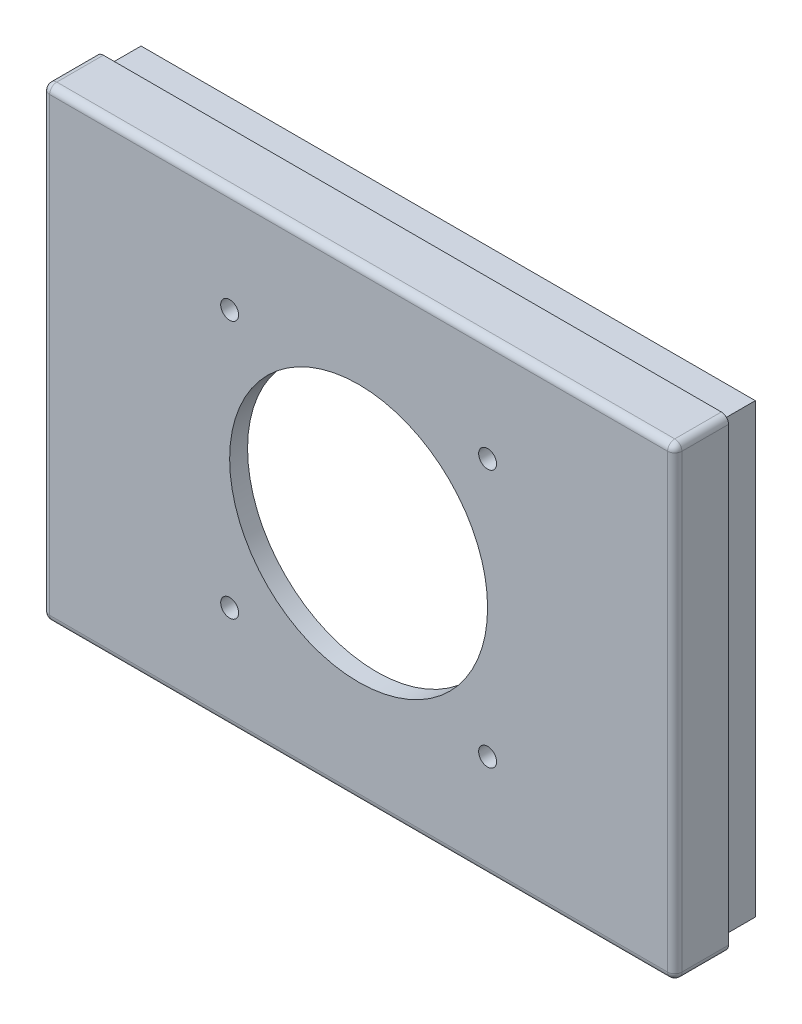
SolidWorks part; units mm, degrees
ref_plane "Front Plane" through (0, 0, 0) normal (0, 0, 1) x (1, 0, 0)
ref_plane "Top Plane" through (0, 0, 0) normal (0, 1, 0) x (1, 0, 0)
ref_plane "Right Plane" through (0, 0, 0) normal (1, 0, 0) x (0, 0, -1)
sketch "Sketch4" plane through (0, 0, 10) normal (0, 0, 1) x (1, 0, 0)
  line L1 (-25, 104.883) -> (151.492, 104.883)
  line L2 (-25, 104.883) -> (-25, -25)
  line L3 (-25, -25) -> (151.492, -25)
  line L4 (151.492, 104.883) -> (151.492, -25)
extrude "Boss-Extrude1" add sketch "Sketch4" along normal blind 25
sketch "Sketch5" plane through (0, 0, 10) normal (0, 0, -1) x (-1, 0, 0)
  line L0 (-146.492, 99.883) -> (-146.492, -20)
  line L1 (-151.492, 104.883) -> (25, 104.883)
  line L2 (-151.492, 104.883) -> (-151.492, -25)
  line L3 (-151.492, -25) -> (25, -25)
  line L4 (25, 104.883) -> (25, -25)
  line L5 (-146.492, -20) -> (20, -20)
  line L6 (20, 99.883) -> (20, -20)
  line L7 (-146.492, 99.883) -> (20, 99.883)
  dimension "D1" = 5
extrude "Cut-Extrude1" cut sketch "Sketch5" against normal blind 20 flip side to cut
sketch "Sketch7" plane through (0, 0, 10) normal (0, 0, -1) x (-1, 0, 0)
  line L0 (25, -25) -> (-151.492, -25) construction
  line L1 (-151.492, 104.883) -> (25, 104.883)
  line L2 (-151.492, 104.883) -> (-151.492, -25)
  line L3 (-151.492, -25) -> (25, -25)
  line L4 (25, 104.883) -> (25, -25)
  line L5 (-148.972, 102.363) -> (-148.972, -22.48)
  line L6 (-148.972, -22.48) -> (22.48, -22.48)
  line L7 (22.48, 102.363) -> (22.48, -22.48)
  line L8 (-148.972, 102.363) -> (22.48, 102.363)
  dimension "D1" = 2.52
extrude "Cut-Extrude2" cut sketch "Sketch7" against normal blind 10
sketch "Sketch11" plane through (0, 0, 35) normal (0, 0, 1) x (1, 0, 0)
  line L0 (63.246, 104.883) -> (63.246, -25) construction
  line L1 (151.492, 104.883) -> (-25, 104.883) construction
  line L2 (-25, -25) -> (151.492, -25) construction
  line L3 (-25, 39.9415) -> (151.492, 39.9415) construction
  line L4 (-25, 104.883) -> (-25, -25) construction
  line L5 (151.492, -25) -> (151.492, 104.883) construction
  line L7 (27.246, 75.9415) -> (99.246, 75.9415)
  line L8 (27.246, 75.9415) -> (27.246, 3.9415)
  line L9 (27.246, 3.9415) -> (99.246, 3.9415)
  line L10 (99.246, 75.9415) -> (99.246, 3.9415)
  line L11 (27.246, 75.9415) -> (99.246, 3.9415) construction
  line L12 (27.246, 3.9415) -> (99.246, 75.9415) construction
  point P12 (63.246, 39.9415)
  dimension "D1" = 72
  dimension "D2" = 72
sketch "Sketch12" plane through (0, 0, 35) normal (0, 0, 1) x (1, 0, 0)
  circle A0 centre (63.246, 39.9415) radius 36
extrude "Cut-Extrude3" cut sketch "Sketch12" against normal blind 15
sketch "Sketch13" plane through (0, 0, 35) normal (0, 0, 1) x (1, 0, 0)
  circle A0 centre (27.246, 75.9415) radius 2.5
  circle A1 centre (99.246, 75.9415) radius 2.5
  circle A2 centre (99.246, 3.9415) radius 2.5
  circle A3 centre (27.246, 3.9415) radius 2.5
  dimension "D1" = 2
  dimension "D2" = 2
extrude "Cut-Extrude4" cut sketch "Sketch13" against normal blind 15
fillet "Fillet1" radius 2 8 edges at (63.246, 104.883, 35) (-25, 39.9415, 35) (-25, 104.883, 27.5) (151.492, 104.883, 27.5) (151.492, 39.9415, 35) (151.492, -25, 27.5) (63.246, -25, 35) (-25, -25, 27.5)
